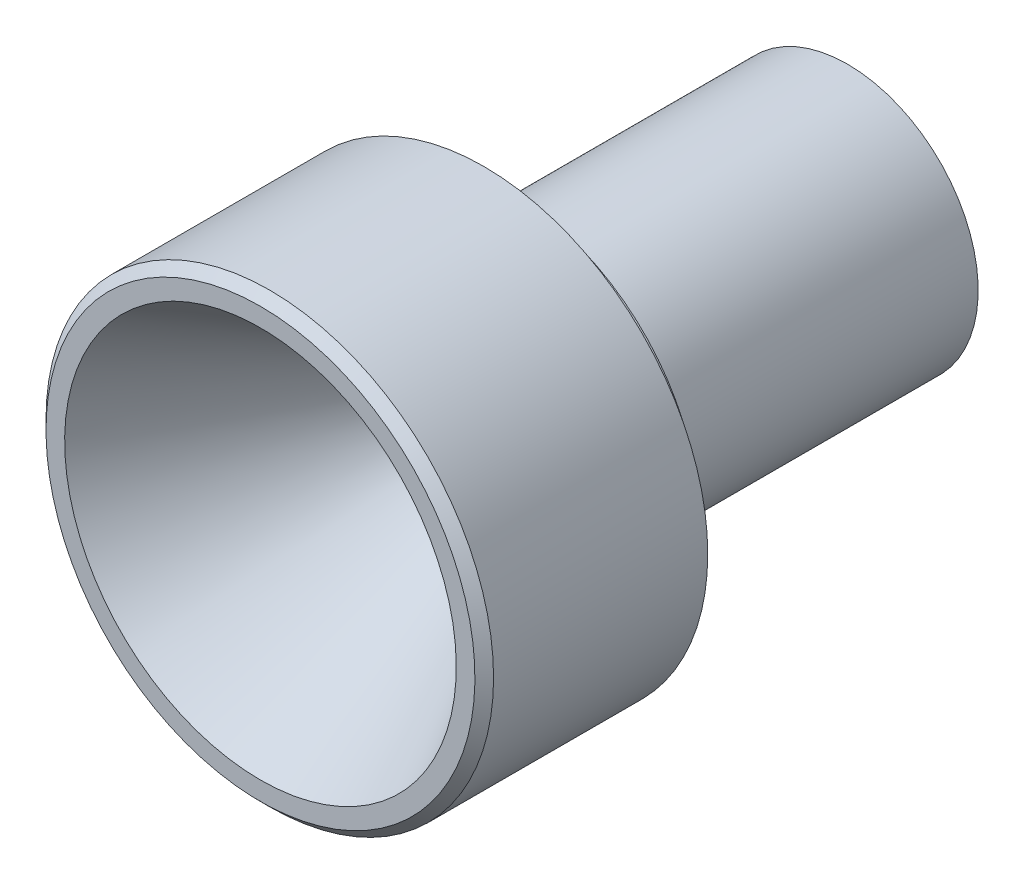
SolidWorks part; units mm, degrees
material "AISI 1035 Acier (SS)"
ref_plane "Plan de face" through (0, 0, 0) normal (0, 0, 1) x (1, 0, 0)
ref_plane "Plan de dessus" through (0, 0, 0) normal (0, 1, 0) x (1, 0, 0)
ref_plane "Plan de droite" through (0, 0, 0) normal (1, 0, 0) x (0, 0, -1)
sketch "Esquisse1" plane through (0, 0, 0) normal (1, 0, 0) x (0, 0, -1)
  line L0 (-15.742, 0) -> (15.742, 0) construction
  line L3 (15.742, 4.5) -> (3.9804, 2)
  line L4 (-15.742, 12) -> (-15.742, 10.5)
  line L5 (-15.742, 10.5) -> (-1.0196, 2)
  line L17 (15.742, 7) -> (15.742, 4.5)
  line L18 (-2.258, 7) -> (15.742, 7)
  line L20 (3.9804, 2) -> (-1.0196, 2)
  line L21 (-3.758, 12) -> (-3.758, 10)
  line L22 (-3.758, 10) -> (-2.258, 10)
  line L23 (-2.258, 10) -> (-2.258, 7)
  line L27 (-15.742, 12) -> (-3.758, 12)
  point P8 (-15.742, 12.1153)
  point P12 (-15.742, 12)
  point P13 (-3.758, 11.5859)
  dimension "D2" = 12
  dimension "D3" = 5
  dimension "D4" = 4.5
  dimension "D5" = 12
  dimension "D6" = 30
  dimension "D7" = 1.5
  dimension "D8" = 2
  dimension "D9" = 2
  dimension "D10" = 18
  dimension "D13" = 10.5
  dimension "D15" = 2.5
revolve "Révolution1" add sketch "Esquisse1" angle 360 about L0
chamfer "Chanfrein1" distance 0.5 angle 45 1 edges at (0, -12, 15.742)
